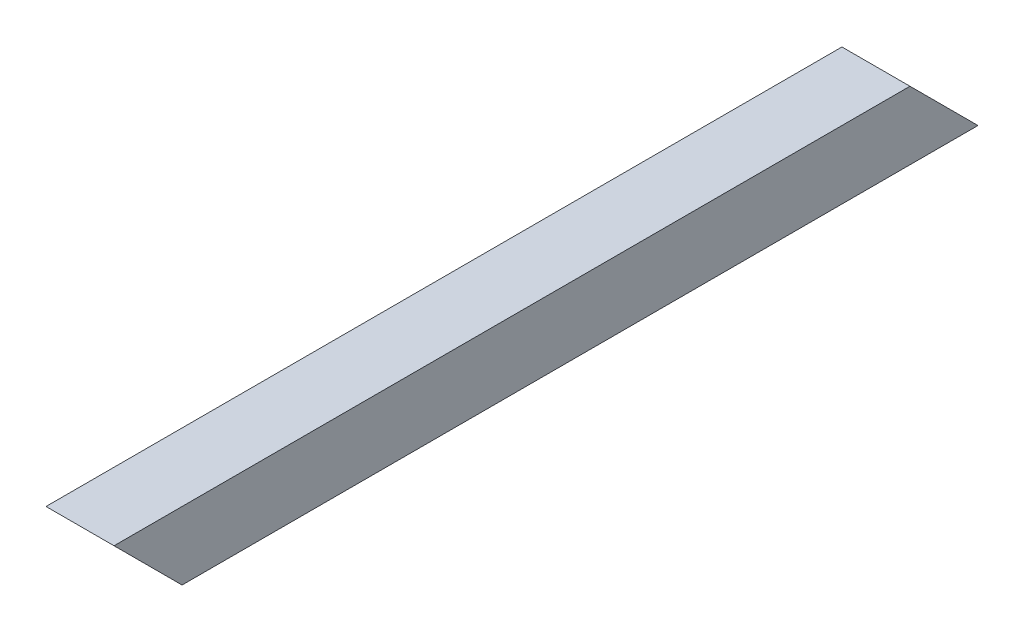
SolidWorks part; units mm, degrees
ref_plane "Front Plane" through (0, 0, 0) normal (0, 0, 1) x (1, 0, 0)
ref_plane "Top Plane" through (0, 0, 0) normal (0, 1, 0) x (1, 0, 0)
ref_plane "Right Plane" through (0, 0, 0) normal (1, 0, 0) x (0, 0, -1)
sketch "Sketch3" plane through (0, 0, 0) normal (0, 0, 1) x (1, 0, 0)
  line L1 (-15.4656, 10.9459) -> (9.9344, 10.9459)
  line L2 (-15.4656, 10.9459) -> (-15.4656, -14.4541)
  line L3 (-15.4656, -14.4541) -> (9.9344, -14.4541)
  line L4 (9.9344, 10.9459) -> (9.9344, -14.4541)
  line L5 (-12.2906, 7.7709) -> (6.7594, 7.7709)
  line L6 (-12.2906, 7.7709) -> (-12.2906, -11.2791)
  line L7 (-12.2906, -11.2791) -> (6.7594, -11.2791)
  line L8 (6.7594, 7.7709) -> (6.7594, -11.2791)
  dimension "D1" = 25.4
  dimension "D2" = 25.4
  dimension "D3" = 3.175
  dimension "D4" = 3.175
  dimension "D5" = 3.175
extrude "Boss-Extrude2" add sketch "Sketch3" along normal blind 322.58
sketch "Sketch4" plane through (-15.4656, 0, 0) normal (-1, 0, 0) x (0, 0, 1)
  line L0 (322.58, 10.9459) -> (297.18, -14.4541)
  line L1 (322.58, -14.4541) -> (0, -14.4541) construction
  line L2 (322.58, 10.9459) -> (322.58, -14.4541) construction
  line L3 (322.58, 10.9459) -> (322.58, -14.4541)
  line L4 (322.58, -14.4541) -> (297.18, -14.4541)
  dimension "D1" = 45
extrude "Cut-Extrude2" cut sketch "Sketch4" against normal blind 299.72
sketch "Sketch5" plane through (-15.4656, 0, 0) normal (-1, 0, 0) x (0, 0, 1)
  line L0 (0, -14.4541) -> (25.4, 10.9459)
  line L1 (322.58, 10.9459) -> (0, 10.9459) construction
  line L2 (0, 10.9459) -> (0, -14.4541) construction
  line L3 (25.4, 10.9459) -> (0, 10.9459)
  line L4 (0, 10.9459) -> (0, -14.4541)
  dimension "D1" = 45
extrude "Cut-Extrude3" cut sketch "Sketch5" against normal blind 25.4
